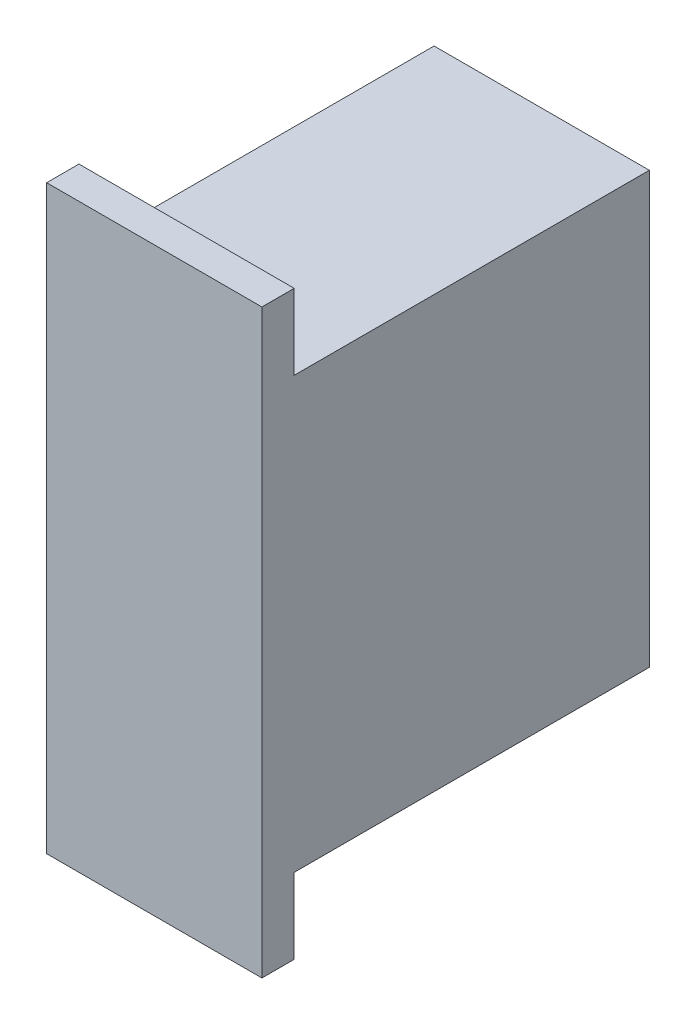
SolidWorks part; units mm, degrees
ref_plane "Front Plane" through (0, 0, 0) normal (0, 0, 1) x (1, 0, 0)
ref_plane "Top Plane" through (0, 0, 0) normal (0, 1, 0) x (1, 0, 0)
ref_plane "Right Plane" through (0, 0, 0) normal (1, 0, 0) x (0, 0, -1)
sketch "Sketch1" plane through (0, 0, 0) normal (0, 0, 1) x (1, 0, 0)
  line L1 (-10, -20) -> (10, -20)
  line L2 (-10, -20) -> (-10, 20)
  line L3 (-10, 20) -> (10, 20)
  line L4 (10, -20) -> (10, 20)
  line L5 (-10, -20) -> (10, 20) construction
  line L6 (-10, 20) -> (10, -20) construction
  point P0 (0, 0)
  dimension "D1" = 20
  dimension "D2" = 40
extrude "Boss-Extrude1" add sketch "Sketch1" along normal blind 36
sketch "Sketch2" plane through (0, 0, 36) normal (0, 0, 1) x (1, 0, 0)
  line L0 (11, 0) -> (-11, 0) construction
  line L1 (-10, 20) -> (10, 20)
  line L2 (-10, 20) -> (-10, 27)
  line L3 (-10, 27) -> (10, 27)
  line L4 (10, 20) -> (10, 27)
  line L5 (-10, -27) -> (10, -27)
  line L6 (10, -20) -> (10, -27)
  line L7 (-10, -20) -> (10, -20)
  line L8 (-10, -20) -> (-10, -27)
  dimension "D1" = 7
  dimension "D2" = 20
extrude "Boss-Extrude5" add sketch "Sketch2" against normal blind 3
